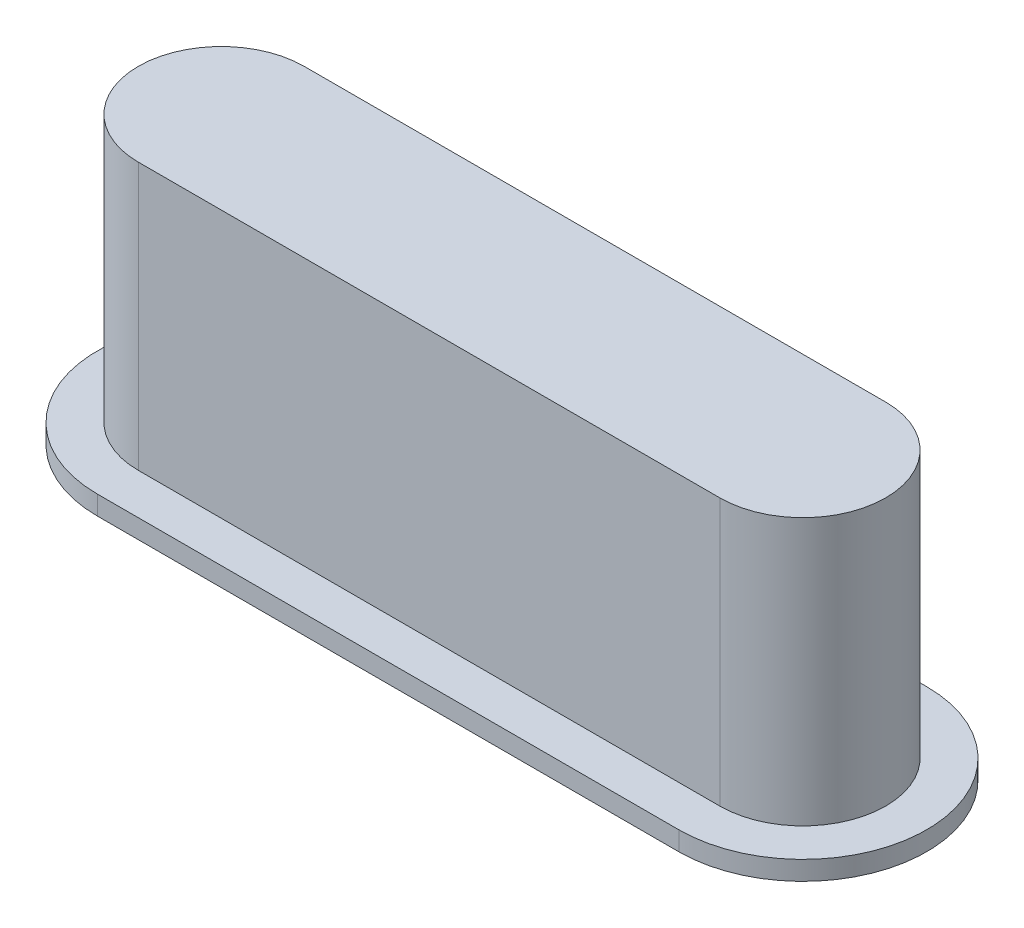
SolidWorks part; units mm, degrees
ref_plane "Front Plane" through (0, 0, 0) normal (0, 0, 1) x (1, 0, 0)
ref_plane "Top Plane" through (0, 0, 0) normal (0, 1, 0) x (1, 0, 0)
ref_plane "Right Plane" through (0, 0, 0) normal (1, 0, 0) x (0, 0, -1)
sketch "Sketch1" plane through (0, 0, 0) normal (0, 1, 0) x (1, 0, 0)
  line L0 (-3.8735, 0) -> (3.8735, 0) construction
  line L1 (-3.8735, 1.1049) -> (3.8735, 1.1049)
  line L2 (-3.8735, -1.1049) -> (3.8735, -1.1049)
  arc A0 (-3.8735, 1.1049) -> (-3.8735, -1.1049) centre (-3.8735, 0) ccw
  arc A1 (3.8735, -1.1049) -> (3.8735, 1.1049) centre (3.8735, 0) ccw
  point P2 (0, 0)
  dimension "D1" = 9.9568
  dimension "D2" = 2.2098
extrude "Boss-Extrude1" add sketch "Sketch1" along normal blind 3.556
sketch "Sketch3" plane through (0, 0, 0) normal (0, 1, 0) x (1, 0, 0)
  line L0 (-3.8735, 0) -> (3.8735, 0) construction
  line L1 (-3.8735, 1.651) -> (3.8735, 1.651)
  line L2 (-3.8735, -1.651) -> (3.8735, -1.651)
  arc A0 (-3.8735, 1.651) -> (-3.8735, -1.651) centre (-3.8735, 0) ccw
  arc A1 (3.8735, -1.651) -> (3.8735, 1.651) centre (3.8735, 0) ccw
  point P2 (0, 0)
  point P8 (3.8735, 0)
  dimension "D1" = 3.302
extrude "Boss-Extrude2" add sketch "Sketch3" against normal blind 0.254
